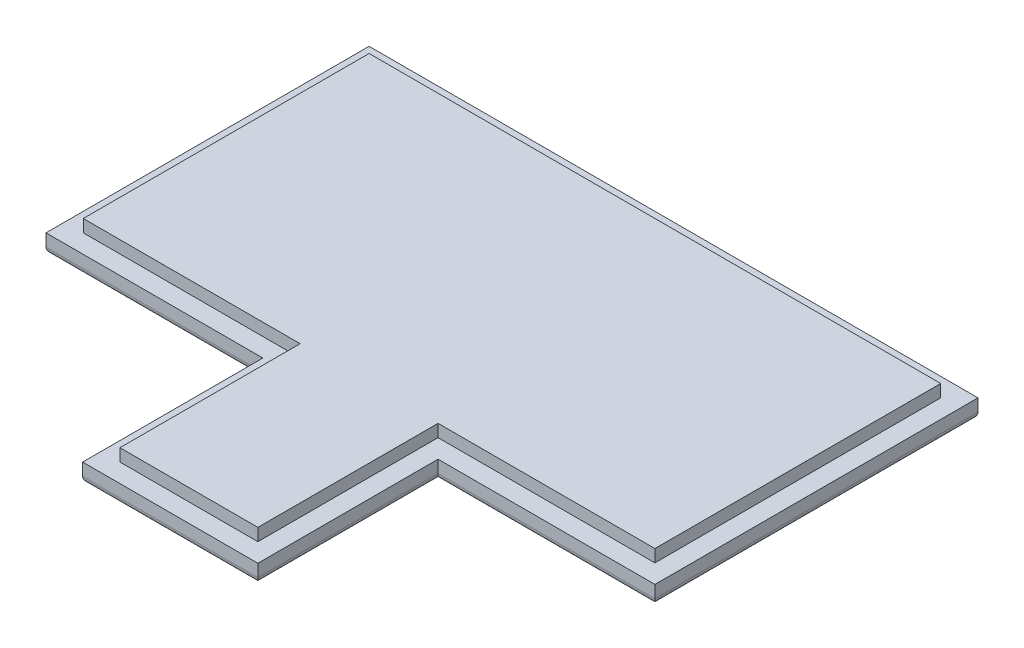
SolidWorks part; units mm, degrees
ref_plane "前视基准面" through (0, 0, 0) normal (0, 0, 1) x (1, 0, 0)
ref_plane "上视基准面" through (0, 0, 0) normal (0, 1, 0) x (1, 0, 0)
ref_plane "右视基准面" through (0, 0, 0) normal (1, 0, 0) x (0, 0, -1)
other "Configuration Table"
sketch "草图1" plane through (0, 0, 0) normal (0, 1, 0) x (1, 0, 0)
  line L0 (-5.55, -13) -> (5.55, -13) construction
  line L1 (-23, 11.5) -> (23, 11.5) construction
  line L2 (-23, 11.5) -> (-23, -11.5) construction
  line L3 (-23, -11.5) -> (23, -11.5) construction
  line L4 (23, 11.5) -> (23, -11.5) construction
  line L5 (-23, 11.5) -> (23, -11.5) construction
  line L6 (-23, -11.5) -> (23, 11.5) construction
  line L7 (-24.5, 13) -> (24.5, 13)
  line L8 (-24.5, 13) -> (-24.5, -13)
  line L9 (-24.5, -13) -> (-7.05, -13)
  line L10 (24.5, 13) -> (24.5, -13)
  line L11 (-24.5, 13) -> (24.5, -13) construction
  line L12 (-24.5, -13) -> (24.5, 13) construction
  line L13 (-5.55, -13) -> (-5.55, -26) construction
  line L14 (-5.55, -26) -> (5.55, -26) construction
  line L15 (5.55, -26) -> (5.55, -13) construction
  line L16 (-4.05, -11.5) -> (4.05, -11.5) construction
  line L17 (-4.05, -11.5) -> (-4.05, -24.5) construction
  line L18 (-4.05, -24.5) -> (4.05, -24.5) construction
  line L19 (4.05, -24.5) -> (4.05, -11.5) construction
  line L20 (-7.05, -13) -> (-7.05, -26)
  line L21 (7.05, -13) -> (24.5, -13)
  line L22 (-5.55, -26) -> (5.55, -26) construction
  line L23 (7.05, -26) -> (7.05, -13)
  line L24 (-7.05, -26) -> (-7.05, -27.5)
  line L25 (-7.05, -27.5) -> (7.05, -27.5)
  line L26 (7.05, -27.5) -> (7.05, -26)
  line L28 (-4.05, -26) -> (4.05, -26) construction
  point P0 (0, 0)
  point P6 (0, 0)
  point P14 (0, -13)
  point P19 (0, -11.5)
  dimension "D1" = 46
  dimension "D2" = 23
  dimension "D3" = 1.5
  dimension "D4" = 1.5
  dimension "D5" = 11.1
  dimension "D6" = 13
  dimension "D7" = 8.1
  dimension "D8" = 1.5
  dimension "D9" = 1.5
  dimension "D10" = 1.5
  dimension "D11" = 1.5
  dimension "D12" = 1.5
extrude "凸台-拉伸1" add sketch "草图1" along normal blind 1.5
ref_plane "基准面1" through (0, 1.5, 0) normal (0, 1, 0) x (1, 0, 0)
sketch "草图2" plane through (0, 1.5, 0) normal (0, 1, 0) x (1, 0, 0)
  line L0 (23, 11.5) -> (23, -11.5) construction
  line L1 (-23, -11.5) -> (23, -11.5) construction
  line L2 (-23, 11.5) -> (-23, -11.5) construction
  line L3 (-23, 11.5) -> (23, 11.5) construction
  line L4 (23, 11.5) -> (23, -11.5)
  line L5 (-23, -11.5) -> (-5.55, -11.5)
  line L6 (-23, 11.5) -> (-23, -11.5)
  line L7 (-23, 11.5) -> (23, 11.5)
  line L8 (-4.05, -24.5) -> (4.05, -24.5) construction
  line L9 (4.05, -24.5) -> (4.05, -11.5) construction
  line L10 (-4.05, -11.5) -> (-4.05, -24.5) construction
  line L11 (-4.05, -24.5) -> (4.05, -24.5) construction
  line L12 (4.05, -24.5) -> (4.05, -11.5) construction
  line L13 (-4.05, -11.5) -> (-4.05, -24.5) construction
  line L14 (5.55, -11.5) -> (23, -11.5)
  line L15 (5.55, -26) -> (5.55, -13) construction
  line L16 (-5.55, -13) -> (-5.55, -26) construction
  line L17 (5.55, -24.5) -> (5.55, -13)
  line L18 (-5.55, -13) -> (-5.55, -24.5)
  line L20 (-5.55, -11.5) -> (-5.55, -13)
  line L21 (5.55, -13) -> (5.55, -11.5)
  line L22 (-5.55, -24.5) -> (-5.55, -26)
  line L23 (-5.55, -26) -> (5.55, -26)
  line L24 (5.55, -26) -> (5.55, -24.5)
  line L25 (-7.05, -27.5) -> (7.05, -27.5) construction
  dimension "D1" = 1.5
extrude "凸台-拉伸2" add sketch "草图2" along normal blind 1
fillet "圆角1" radius 0.5 8 edges at (24.5, 0, 0) (0, 0, -13) (-24.5, 0, 0) (-15.775, 0, 13) (15.775, 0, 13) (-7.05, 0, 20.25) (7.05, 0, 20.25) (0, 0, 27.5)
